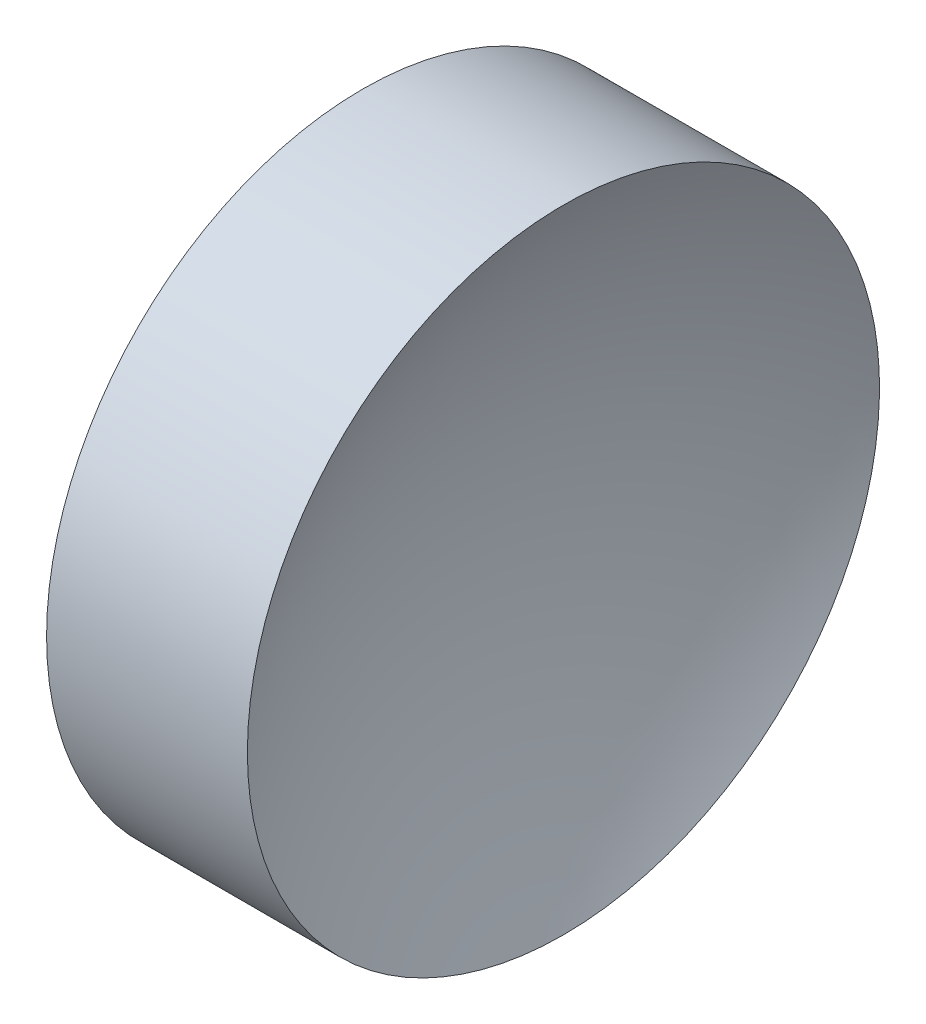
SolidWorks part; units mm, degrees
ref_plane "前视基准面" through (0, 0, 0) normal (0, 0, 1) x (1, 0, 0)
ref_plane "上视基准面" through (0, 0, 0) normal (0, 1, 0) x (1, 0, 0)
ref_plane "右视基准面" through (0, 0, 0) normal (1, 0, 0) x (0, 0, -1)
sketch "草图1" plane through (0, 0, 0) normal (0, 0, 1) x (1, 0, 0)
  line L0 (106.1247, 65.2226) -> (139.1613, 65.2226) construction
  line L1 (118.8409, 65.2226) -> (121.3409, 65.2226)
  line L3 (120.0909, 85.2226) -> (126.4445, 85.2226)
  line L4 (120.0909, 85.2226) -> (113.7374, 85.2226)
  arc A0 (118.8409, 65.2226) -> (113.7374, 85.2226) centre (77.1009, 65.2226) ccw
  arc A1 (126.4445, 85.2226) -> (121.3409, 65.2226) centre (163.0809, 65.2226) ccw
revolve "旋转1" add sketch "草图1" angle 360 about L0
